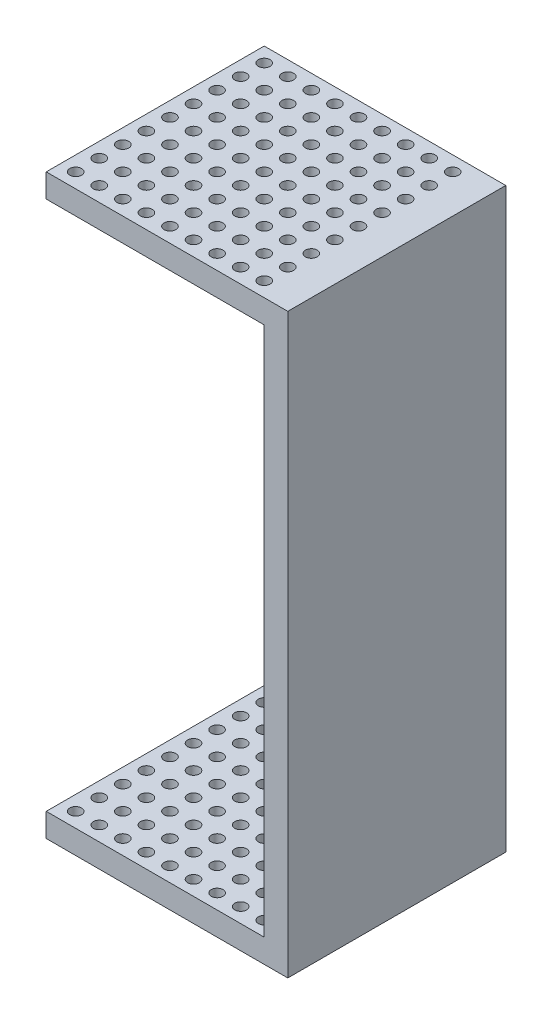
SolidWorks part; units mm, degrees
ref_plane "Front Plane" through (0, 0, 0) normal (0, 0, 1) x (1, 0, 0)
ref_plane "Top Plane" through (0, 0, 0) normal (0, 1, 0) x (1, 0, 0)
ref_plane "Right Plane" through (0, 0, 0) normal (1, 0, 0) x (0, 0, -1)
sketch "Sketch1" plane through (0, 0, 0) normal (0, 1, 0) x (1, 0, 0)
  line L1 (10.25, -9.25) -> (-10.25, -9.25)
  line L2 (10.25, -9.25) -> (10.25, 9.25)
  line L3 (10.25, 9.25) -> (-10.25, 9.25)
  line L4 (-10.25, -9.25) -> (-10.25, 9.25)
  line L5 (10.25, -9.25) -> (-10.25, 9.25) construction
  line L6 (10.25, 9.25) -> (-10.25, -9.25) construction
  point P0 (0, 0)
  dimension "D1" = 20.5
  dimension "D2" = 18.5
extrude "Boss-Extrude1" add sketch "Sketch1" along normal blind 2
sketch "Sketch2" plane through (0, 2, 0) normal (0, 1, 0) x (1, 0, 0)
  line L0 (-10.25, 9.25) -> (10.25, -9.25) construction
  line L1 (10.25, 9.25) -> (-10.25, -9.25) construction
  line L3 (10.25, 9.25) -> (-10.25, 9.25) construction
  line L5 (10.25, -9.25) -> (8.25, -9.25)
  line L7 (8.25, -9.25) -> (8.25, 9.25)
  line L8 (8.25, 9.25) -> (10.25, 9.25)
  line L9 (-10.25, -9.25) -> (10.25, -9.25) construction
  line L12 (10.25, 9.25) -> (10.25, -9.25)
  dimension "D2" = 2
extrude "Boss-Extrude2" add sketch "Sketch2" along normal blind 45
sketch "Sketch3" plane through (0, 0, 0) normal (0, -1, 0) x (1, 0, 0)
  line L0 (-9, 8) -> (-9, 9.25) construction
  line L1 (10.25, 9.25) -> (-10.25, -9.25) construction
  line L2 (-10.25, -9.25) -> (-10.25, 9.25) construction
  line L7 (-10.25, 9.25) -> (10.25, 9.25) construction
  circle A0 centre (-9, 8) radius 0.5
  circle A1 centre (-7, 8) radius 0.5
  circle A2 centre (-5, 8) radius 0.5
  circle A3 centre (-3, 8) radius 0.5
  circle A4 centre (-1, 8) radius 0.5
  circle A5 centre (1, 8) radius 0.5
  circle A6 centre (3, 8) radius 0.5
  circle A7 centre (5, 8) radius 0.5
  circle A8 centre (7, 8) radius 0.5
  circle A9 centre (-7, 6) radius 0.5
  circle A10 centre (-5, 6) radius 0.5
  circle A11 centre (-3, 6) radius 0.5
  circle A12 centre (-1, 6) radius 0.5
  circle A13 centre (1, 6) radius 0.5
  circle A14 centre (3, 6) radius 0.5
  circle A15 centre (5, 6) radius 0.5
  circle A16 centre (7, 6) radius 0.5
  circle A17 centre (-7, 4) radius 0.5
  circle A18 centre (-5, 4) radius 0.5
  circle A19 centre (-3, 4) radius 0.5
  circle A20 centre (-1, 4) radius 0.5
  circle A21 centre (1, 4) radius 0.5
  circle A22 centre (3, 4) radius 0.5
  circle A23 centre (5, 4) radius 0.5
  circle A24 centre (7, 4) radius 0.5
  circle A25 centre (-7, 2) radius 0.5
  circle A26 centre (-5, 2) radius 0.5
  circle A27 centre (-3, 2) radius 0.5
  circle A28 centre (-1, 2) radius 0.5
  circle A29 centre (1, 2) radius 0.5
  circle A30 centre (3, 2) radius 0.5
  circle A31 centre (5, 2) radius 0.5
  circle A32 centre (7, 2) radius 0.5
  circle A33 centre (-7, 0) radius 0.5
  circle A34 centre (-5, 0) radius 0.5
  circle A35 centre (-3, 0) radius 0.5
  circle A36 centre (-1, 0) radius 0.5
  circle A37 centre (1, 0) radius 0.5
  circle A38 centre (3, 0) radius 0.5
  circle A39 centre (5, 0) radius 0.5
  circle A40 centre (7, 0) radius 0.5
  circle A41 centre (-7, -2) radius 0.5
  circle A42 centre (-5, -2) radius 0.5
  circle A43 centre (-3, -2) radius 0.5
  circle A44 centre (-1, -2) radius 0.5
  circle A45 centre (1, -2) radius 0.5
  circle A46 centre (3, -2) radius 0.5
  circle A47 centre (5, -2) radius 0.5
  circle A48 centre (7, -2) radius 0.5
  circle A49 centre (-7, -4) radius 0.5
  circle A50 centre (-5, -4) radius 0.5
  circle A51 centre (-3, -4) radius 0.5
  circle A52 centre (-1, -4) radius 0.5
  circle A53 centre (1, -4) radius 0.5
  circle A54 centre (3, -4) radius 0.5
  circle A55 centre (5, -4) radius 0.5
  circle A56 centre (7, -4) radius 0.5
  circle A57 centre (-7, -6) radius 0.5
  circle A58 centre (-5, -6) radius 0.5
  circle A59 centre (-3, -6) radius 0.5
  circle A60 centre (-1, -6) radius 0.5
  circle A61 centre (1, -6) radius 0.5
  circle A62 centre (3, -6) radius 0.5
  circle A63 centre (5, -6) radius 0.5
  circle A64 centre (7, -6) radius 0.5
  circle A65 centre (-7, -8) radius 0.5
  circle A66 centre (-5, -8) radius 0.5
  circle A67 centre (-3, -8) radius 0.5
  circle A68 centre (-1, -8) radius 0.5
  circle A69 centre (1, -8) radius 0.5
  circle A70 centre (3, -8) radius 0.5
  circle A71 centre (5, -8) radius 0.5
  circle A72 centre (7, -8) radius 0.5
  circle A73 centre (-9, 6) radius 0.5
  circle A74 centre (-9, 4) radius 0.5
  circle A75 centre (-9, 2) radius 0.5
  circle A76 centre (-9, 0) radius 0.5
  circle A77 centre (-9, -2) radius 0.5
  circle A78 centre (-9, -4) radius 0.5
  circle A79 centre (-9, -6) radius 0.5
  circle A80 centre (-9, -8) radius 0.5
  dimension "D1" = 1
  dimension "D2" = 9
  dimension "D3" = 1.25
  dimension "D4" = 1.25
  dimension "D5" = 9
sketch "Sketch4" plane through (0, 47, 0) normal (0, 1, 0) x (1, 0, 0)
  line L1 (-10.25, 9.25) -> (10.25, 9.25)
  line L2 (-10.25, 9.25) -> (-10.25, -9.25)
  line L3 (-10.25, -9.25) -> (10.25, -9.25)
  line L4 (10.25, 9.25) -> (10.25, -9.25)
  line L5 (-10.25, 9.25) -> (10.25, -9.25) construction
  line L6 (-10.25, -9.25) -> (10.25, 9.25) construction
  point P0 (0, 0)
  dimension "D1" = 20.5
  dimension "D2" = 18.5
extrude "Boss-Extrude3" add sketch "Sketch4" along normal blind 2
extrude "Cut-Extrude1" cut sketch "Sketch3" against normal through all
